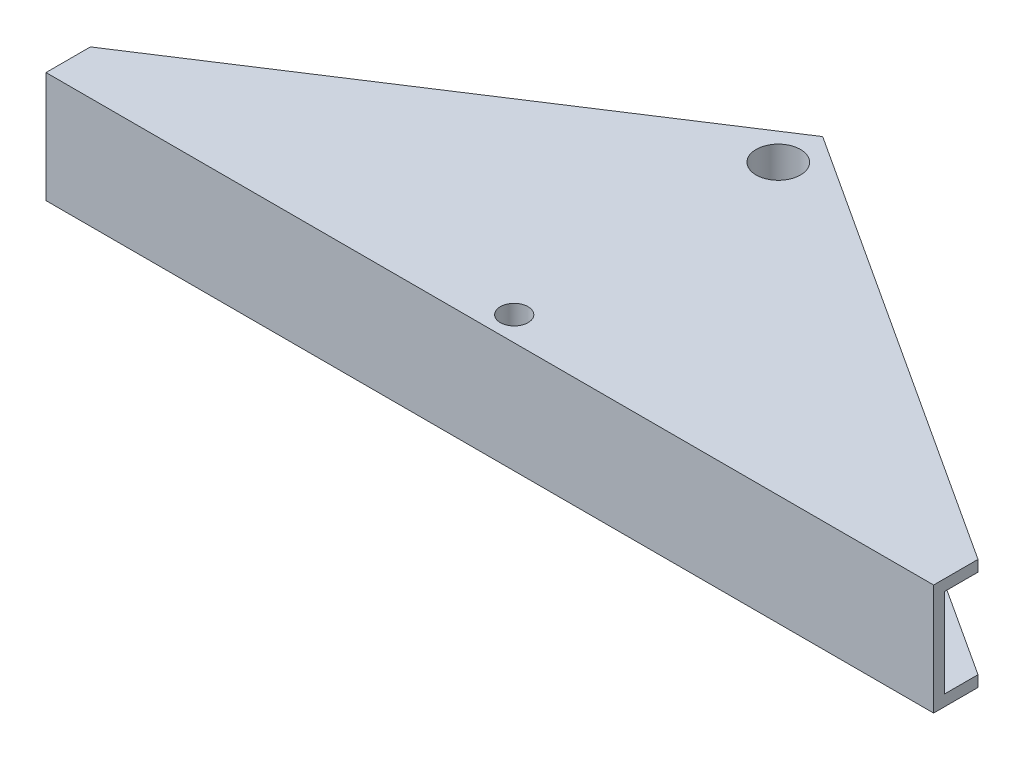
SolidWorks part; units mm, degrees
ref_plane "Front Plane" through (0, 0, 0) normal (0, 0, 1) x (1, 0, 0)
ref_plane "Top Plane" through (0, 0, 0) normal (0, 1, 0) x (1, 0, 0)
ref_plane "Right Plane" through (0, 0, 0) normal (1, 0, 0) x (0, 0, -1)
sketch "Sketch1" plane through (0, 0, 0) normal (0, 1, 0) x (1, 0, 0)
  line L0 (0, 26) -> (-40, 0)
  line L1 (-40, 0) -> (-40, -4)
  line L2 (40, 0) -> (0, 26)
  line L3 (-40, -4) -> (40, -4)
  line L4 (40, -4) -> (40, 0)
  circle A0 centre (0, 22) radius 2
  circle A1 centre (0, -1.8) radius 1.25
  point P10 (0, 26)
  point P11 (-39.8178, 5.2859)
  point P12 (0, 0)
  dimension "D3" = 4
  dimension "D5" = 4
  dimension "D6" = 2.5
  dimension "D1" = 26
  dimension "D2" = 80
  dimension "D4" = 22
  dimension "D7" = 1.8
extrude "Boss-Extrude1" add sketch "Sketch1" along normal blind 10
ref_plane "Plane1" through (0, 9, 0) normal (0, 1, 0) x (1, 0, 0)
sketch "Sketch2" plane through (0, 9, 0) normal (0, 1, 0) x (1, 0, 0)
  line L0 (-3, 26) -> (-7.7469, 2)
  line L1 (-7.7469, 2) -> (-40, -3)
  line L2 (-40, -4) -> (40, -4) construction
  line L3 (-40, 0) -> (-40, -4) construction
  line L4 (-40, -3) -> (-40, 3.0638)
  line L5 (-40, 3.0638) -> (-3, 26)
  point P2 (0, 0)
  point P10 (-4.5794, 2.0074)
  point P11 (0, 0)
  point P12 (0, 0)
  point P14 (0, 0)
  point P15 (0, 0)
  point P16 (0, 0)
  point P17 (0, 0)
  dimension "D1" = 3
  dimension "D2" = 26
  dimension "D3" = 1
  dimension "D4" = 6
  dimension "D5" = 110
extrude "Cut-Extrude1" cut sketch "Sketch2" against normal blind 8
mirror "Mirror1" about plane through (0, 0, 0) normal (1, 0, 0) of "Cut-Extrude1"
